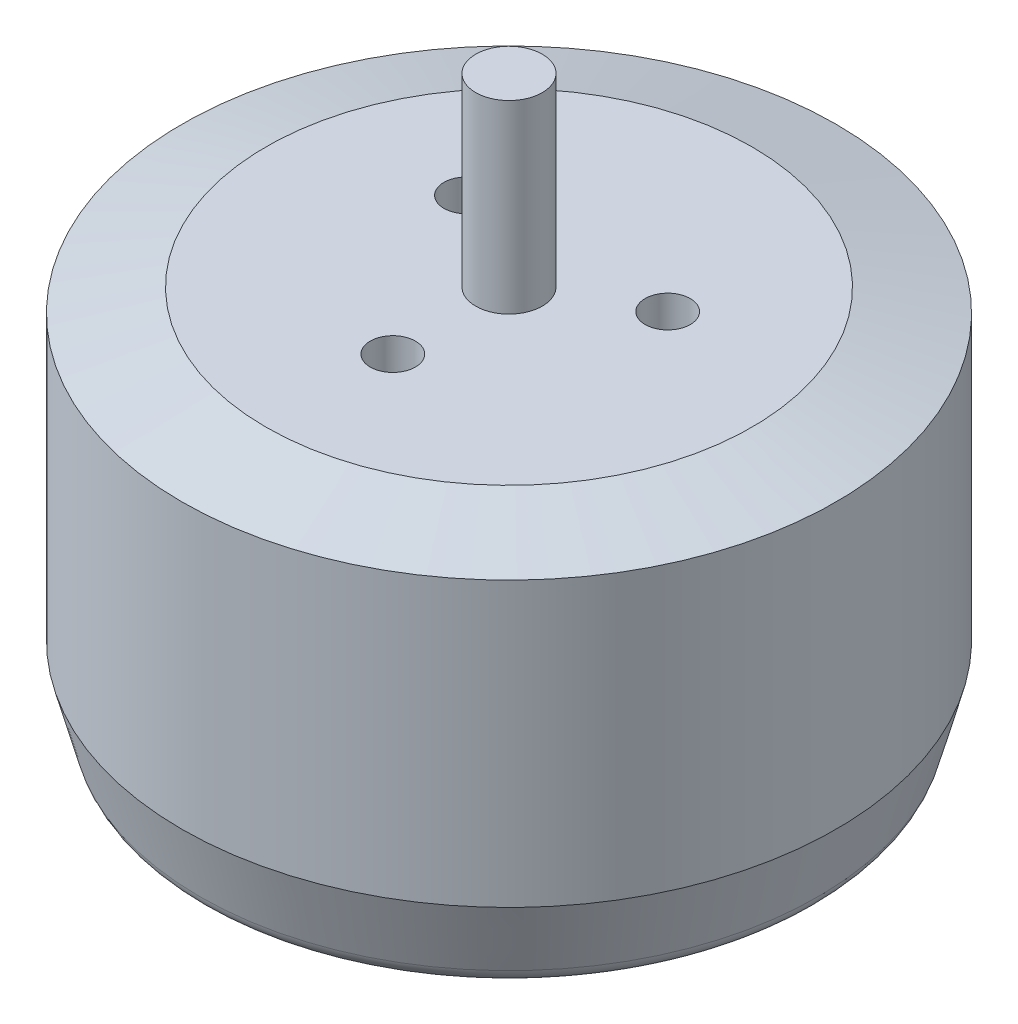
SolidWorks part; units mm, degrees
ref_plane "前视基准面" through (0, 0, 0) normal (0, 0, 1) x (1, 0, 0)
ref_plane "上视基准面" through (0, 0, 0) normal (0, 1, 0) x (1, 0, 0)
ref_plane "右视基准面" through (0, 0, 0) normal (1, 0, 0) x (0, 0, -1)
sketch "草图1" plane through (0, 0, 0) normal (0, 1, 0) x (1, 0, 0)
  circle A0 centre (0, 0) radius 14.5
  dimension "D1" = 29
extrude "凸台-拉伸1" add sketch "草图1" along normal blind 17.3
sketch "草图2" plane through (0, 17.3, 0) normal (0, 1, 0) x (1, 0, 0)
  circle A0 centre (0, 0) radius 1.475
  dimension "D1" = 2.95
extrude "凸台-拉伸2" add sketch "草图2" along normal blind 8.2
sketch "草图7" plane through (0, 0, 0) normal (0, -1, 0) x (-1, 0, 0)
  point P0 (0, -8)
  point P1 (0, 8.0006)
  point P2 (9.5, 0)
  point P4 (-9.5, 0)
  dimension "D1" = 8
  dimension "D2" = 16.0006
  dimension "D3" = 9.5
  dimension "D4" = 19
hole_wizard "大小mm Clearance 暗销槽口1" positions "草图8" profile "草图9" size "Ø3.0" standard "ANSI Metric" slot yes
sketch "草图8" plane through (0, 0, 0) normal (0, -1, 0) x (-1, 0, 0)
  point P0 (0, -8)
  point P3 (9.5, 0)
  point P6 (0, 8.0006)
  point P9 (-9.5, 0)
sketch "草图9" plane through (0, 0, 8) normal (1, 0, 0) x (0, 0, -1)
  line L0 (0, 0) -> (0, 3.9013)
  line L1 (0, 3.9013) -> (1.5, 3)
  line L2 (1.5, 3) -> (1.5, 0)
  line L5 (1.5, 0) -> (0, 0)
  line L10 (0, 3.9013) -> (-1.5, 3) construction
  line L11 (0, -6.35) -> (0, 107.95) construction
  dimension "孔直径" = 3
  dimension "孔深度" = 3
  dimension "导头角度" = 118
chamfer "倒角1" distance 1 angle 75 1 edges at (0, 0, 14.5)
fillet "圆角1" radius 1 1 edges at (0, 0, 13.5)
chamfer "倒角2" distance 1 angle 75 1 edges at (0, 17.3, 14.5)
sketch "草图10" plane through (0, 17.3, 0) normal (0, 1, 0) x (1, 0, 0)
  circle A0 centre (0, 0) radius 5.15
  point P2 (0, -5.15)
  point P4 (-4.46, 2.575)
  point P5 (4.46, 2.575)
  dimension "D1" = 10.3
  dimension "D2" = 120
hole_wizard "大小mm Clearance 暗销槽口2" positions "草图11" profile "草图12" size "Ø2.0" standard "ANSI Metric" slot yes
sketch "草图11" plane through (0, 17.3, 0) normal (0, 1, 0) x (1, 0, 0)
  point P0 (-4.46, 2.575)
  point P3 (4.46, 2.575)
  point P6 (0, -5.15)
sketch "草图12" plane through (-4.46, 17.3, -2.575) normal (1, 0, 0) x (0, 0, 1)
  line L0 (0, 0) -> (0, 3.6009)
  line L1 (0, 3.6009) -> (1, 3)
  line L2 (1, 3) -> (1, 0)
  line L5 (1, 0) -> (0, 0)
  line L10 (0, 3.6009) -> (-1, 3) construction
  line L11 (0, -6.35) -> (0, 107.95) construction
  dimension "孔直径" = 2
  dimension "孔深度" = 3
  dimension "导头角度" = 118
